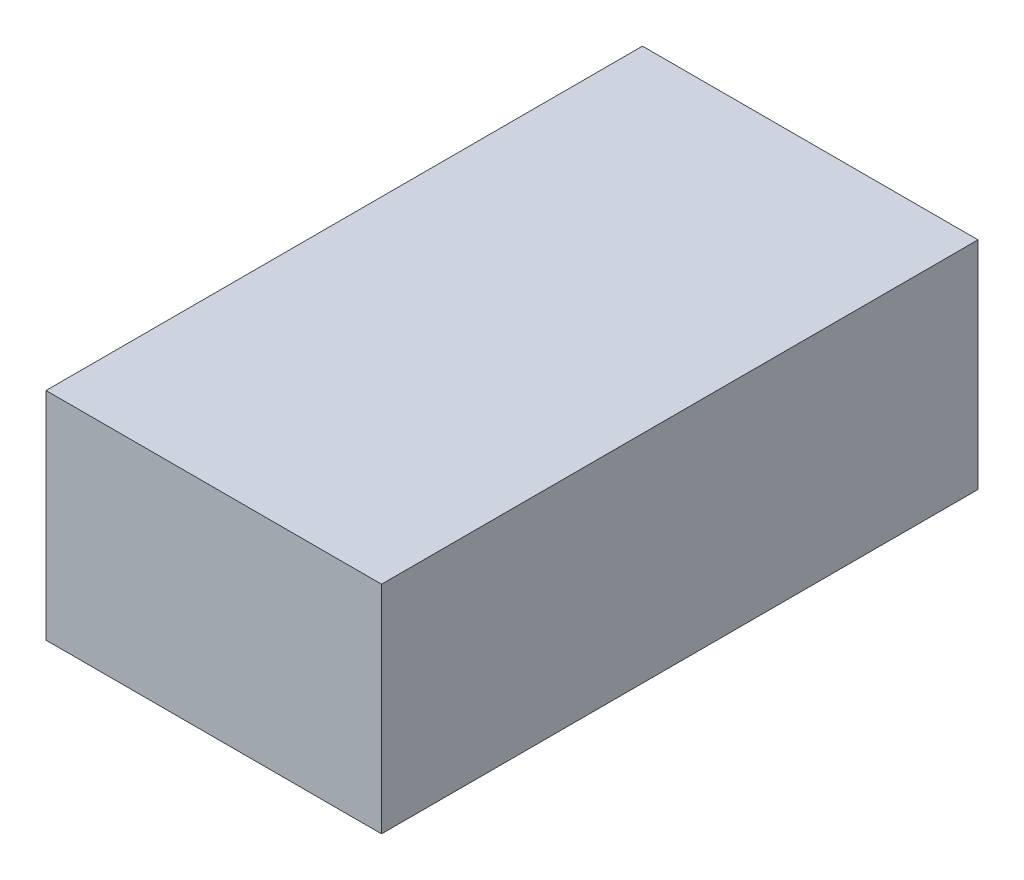
SolidWorks part; units mm, degrees
ref_plane "Front Plane" through (0, 0, 0) normal (0, 0, 1) x (1, 0, 0)
ref_plane "Top Plane" through (0, 0, 0) normal (0, 1, 0) x (1, 0, 0)
ref_plane "Right Plane" through (0, 0, 0) normal (1, 0, 0) x (0, 0, -1)
sketch "Sketch1" plane through (0, 0, 0) normal (0, 1, 0) x (1, 0, 0)
  line L1 (-22.5, -40) -> (22.5, -40)
  line L2 (-22.5, -40) -> (-22.5, 40)
  line L3 (-22.5, 40) -> (22.5, 40)
  line L4 (22.5, -40) -> (22.5, 40)
  line L5 (0, 40) -> (0, -40) construction
  line L6 (-22.5, 0) -> (22.5, 0) construction
  point P0 (0, 0)
  dimension "D1" = 45
  dimension "D2" = 80
extrude "Boss-Extrude1" add sketch "Sketch1" along normal blind 29
